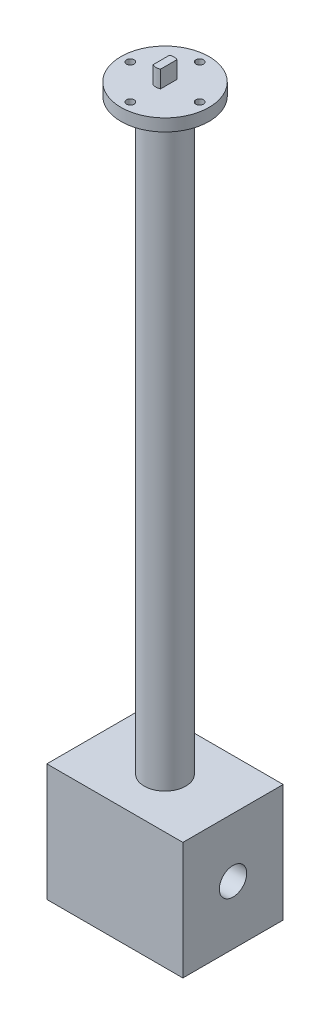
SolidWorks part; units mm, degrees
ref_plane "Front Plane" through (0, 0, 0) normal (0, 0, 1) x (1, 0, 0)
ref_plane "Top Plane" through (0, 0, 0) normal (0, 1, 0) x (1, 0, 0)
ref_plane "Right Plane" through (0, 0, 0) normal (1, 0, 0) x (0, 0, -1)
sketch "Sketch1" plane through (0, 0, 0) normal (0, 1, 0) x (1, 0, 0)
  circle A0 centre (0, 0) radius 22.86
  dimension "D1" = 45.72
extrude "Boss-Extrude1" add sketch "Sketch1" along normal blind 6.35
sketch "Sketch2" plane through (0, 6.35, 0) normal (0, 1, 0) x (1, 0, 0)
  line L0 (1.9685, 4.2668) -> (1.9685, -4.2668)
  line L1 (-1.9685, 4.2668) -> (-1.9685, -4.2668)
  line L2 (0, 0) -> (1.9685, 0) construction
  line L3 (0, 0) -> (-1.9685, 0) construction
  circle A0 centre (0, 0) radius 4.699
  dimension "D1" = 9.398
  dimension "D2" = 1.9685
  dimension "D3" = 1.9685
extrude "Boss-Extrude2" add sketch "Sketch2" along normal blind 8.89 contours L0 A0 L1
sketch "Sketch3" plane through (0, 0, 0) normal (0, -1, 0) x (1, 0, 0)
  circle A0 centre (0, 0) radius 10.795
  dimension "D1" = 21.59
extrude "Boss-Extrude3" add sketch "Sketch3" along normal blind 304.8
chamfer "Chamfer1" distance 3.81 angle 45 1 edges at (0, 0, -10.795)
sketch "Sketch4" plane through (0, 6.35, 0) normal (0, 1, 0) x (1, 0, 0)
  line L0 (0, 0) -> (0, 18) construction
  circle A0 centre (0, 0) radius 18 construction
  dimension "D1" = 36
hole_wizard "5/32 (0.15625) Diameter Hole1" positions "Sketch5" profile "Sketch6" hole size "5/32" standard "ANSI Inch" end condition up to next
sketch "Sketch5" plane through (0, 6.35, 0) normal (0, 1, 0) x (1, 0, 0)
  point P0 (0, 18)
sketch "Sketch6" plane through (0, 6.35, -18) normal (1, 0, 0) x (0, 0, 1)
  line L0 (0, 0) -> (0, 6.351)
  line L1 (0, 6.351) -> (1.9844, 6.351)
  line L2 (1.9844, 6.351) -> (1.9844, 0)
  line L5 (1.9844, 0) -> (0, 0)
  line L11 (0, -6.35) -> (0, 107.95) construction
  dimension "Thru Hole Dia." = 3.9688
  dimension "Thru Hole Depth" = 6.351
pattern_circular "CirPattern1" count 4 over 360 about axis through (0, 0, 0) along (0, 1, 0) of "5/32 (0.15625) Diameter Hole1"
sketch "Sketch7" plane through (0, -304.8, 0) normal (0, -1, 0) x (1, 0, 0)
  line L0 (-35.306, 26.035) -> (35.306, -26.035) construction
  line L1 (-35.306, 26.035) -> (35.306, 26.035)
  line L2 (-35.306, 26.035) -> (-35.306, -26.035)
  line L3 (-35.306, -26.035) -> (35.306, -26.035)
  line L4 (35.306, 26.035) -> (35.306, -26.035)
  point P4 (0, 0)
  dimension "D1" = 52.07
  dimension "D2" = 70.612
extrude "Boss-Extrude4" add sketch "Sketch7" along normal blind 60.96
sketch "Sketch8" plane through (35.306, 0, 0) normal (1, 0, 0) x (0, 0, -1)
  line L0 (-26.035, -304.8) -> (26.035, -365.76) construction
  circle A0 centre (0, -335.28) radius 7.112
  dimension "D1" = 14.224
extrude "Cut-Extrude1" cut sketch "Sketch8" against normal through all
sketch "Sketch9" plane through (0, 0, 0) normal (0, 0, 1) x (1, 0, 0)
  line L0 (-13.97, 7.62) -> (15.3255, 7.62)
  line L1 (15.3255, 7.62) -> (46.9483, 40.64)
  line L2 (46.9483, 40.64) -> (150.114, 40.64)
  line L3 (150.114, 40.64) -> (150.114, 43.815)
  line L4 (150.114, 43.815) -> (45.5927, 43.815)
  line L5 (45.5927, 43.815) -> (13.97, 10.795)
  line L6 (13.97, 10.795) -> (-13.97, 10.795)
  line L7 (-13.97, 10.795) -> (-13.97, 7.62)
  line L8 (-1.9685, 10.795) -> (1.9685, 10.795) construction
  line L9 (-1.9685, 15.24) -> (-1.9685, 6.35) construction
  line L10 (1.9685, 15.24) -> (1.9685, 6.35) construction
  point P14 (0, 10.795)
  point P15 (0, 10.795)
  dimension "D1" = 33.02
  dimension "D2" = 3.175
  dimension "D3" = 3.175
  dimension "D4" = 3.175
  dimension "D5" = 150.114
  dimension "D6" = 45.72
  dimension "D7" = 27.94
extrude "Boss-Extrude5" [suppressed] add sketch "Sketch9" along normal mid plane 22.86
fillet "Fillet1" [suppressed] radius 6.35
equation "\"D2@Sketch2\"=(.37-.215)/2"
